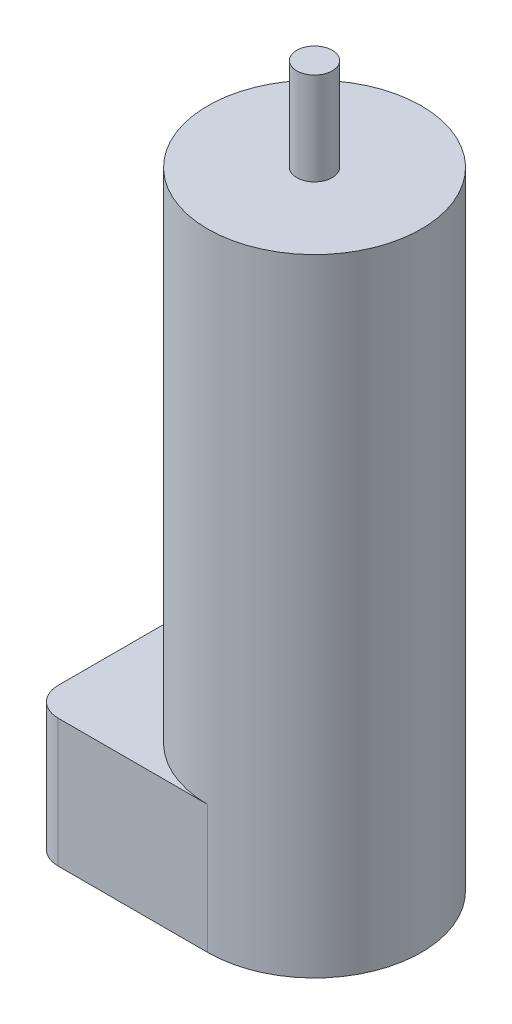
SolidWorks part; units mm, degrees
material "201 Annealed Stainless Steel (SS)"
ref_plane "Front Plane" through (0, 0, 0) normal (0, 0, 1) x (1, 0, 0)
ref_plane "Top Plane" through (0, 0, 0) normal (0, 1, 0) x (1, 0, 0)
ref_plane "Right Plane" through (0, 0, 0) normal (1, 0, 0) x (0, 0, -1)
sketch "Sketch1" plane through (0, 0, 0) normal (0, 1, 0) x (1, 0, 0)
  circle A0 centre (0, 0) radius 15
  dimension "D1" = 30
extrude "Boss-Extrude1" add sketch "Sketch1" along normal blind 88
sketch "Sketch2" plane through (0, 88, 0) normal (0, 1, 0) x (1, 0, 0)
  circle A0 centre (0, 0) radius 2.5
  dimension "D1" = 5
extrude "Boss-Extrude2" add sketch "Sketch2" along normal blind 13
ref_plane "Plane1" through (0, 18, 0) normal (0, -1, 0) x (-1, 0, 0)
sketch "Sketch3" plane through (0, 18, 0) normal (0, -1, 0) x (-1, 0, 0)
  line L0 (0, 15) -> (25, 15)
  line L1 (25, 15) -> (25, -15)
  line L2 (25, -15) -> (0, -15)
  circle A0 centre (0, 0) radius 15 construction
  arc A1 (0, 15) -> (0, -15) centre (0, 0) ccw
  point P7 (25, 0)
  dimension "D1" = 25
extrude "Boss-Extrude3" add sketch "Sketch3" along normal up to surface (18 mm away) up to face at (0, 0, 15)
fillet "Fillet1" radius 4 2 edges at (-25, 9, 15) (-25, 9, -15)
